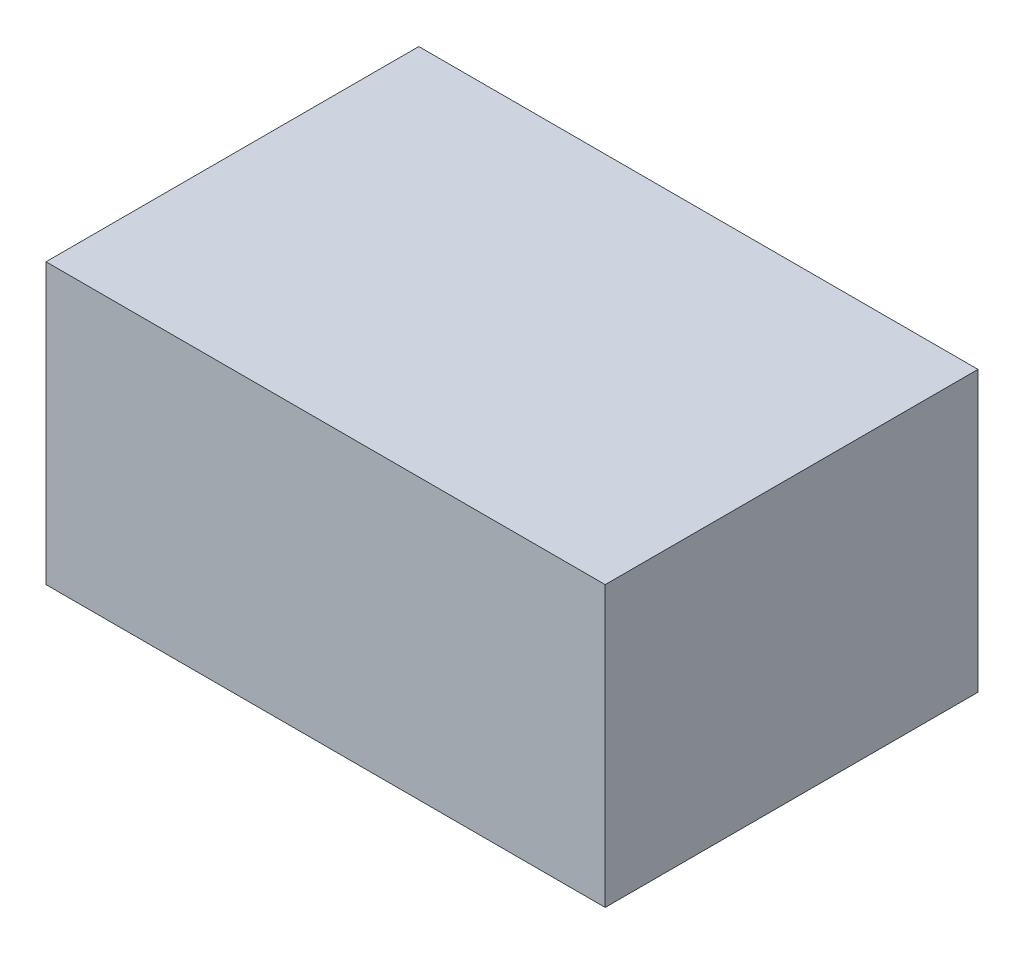
SolidWorks part; units mm, degrees
ref_plane "Front Plane" through (0, 0, 0) normal (0, 0, 1) x (1, 0, 0)
ref_plane "Top Plane" through (0, 0, 0) normal (0, 1, 0) x (1, 0, 0)
ref_plane "Right Plane" through (0, 0, 0) normal (1, 0, 0) x (0, 0, -1)
sketch "Sketch1" plane through (0, 0, 0) normal (0, 0, 1) x (1, 0, 0)
  line L0 (0, 0) -> (600, 0)
  line L1 (600, 0) -> (600, 300)
  line L2 (600, 300) -> (0, 300)
  line L3 (0, 300) -> (0, 0)
  dimension "D1" = 300
  dimension "D2" = 600
  dimension "D3" = 600
extrude "Boss-Extrude1" add sketch "Sketch1" along normal blind 400
